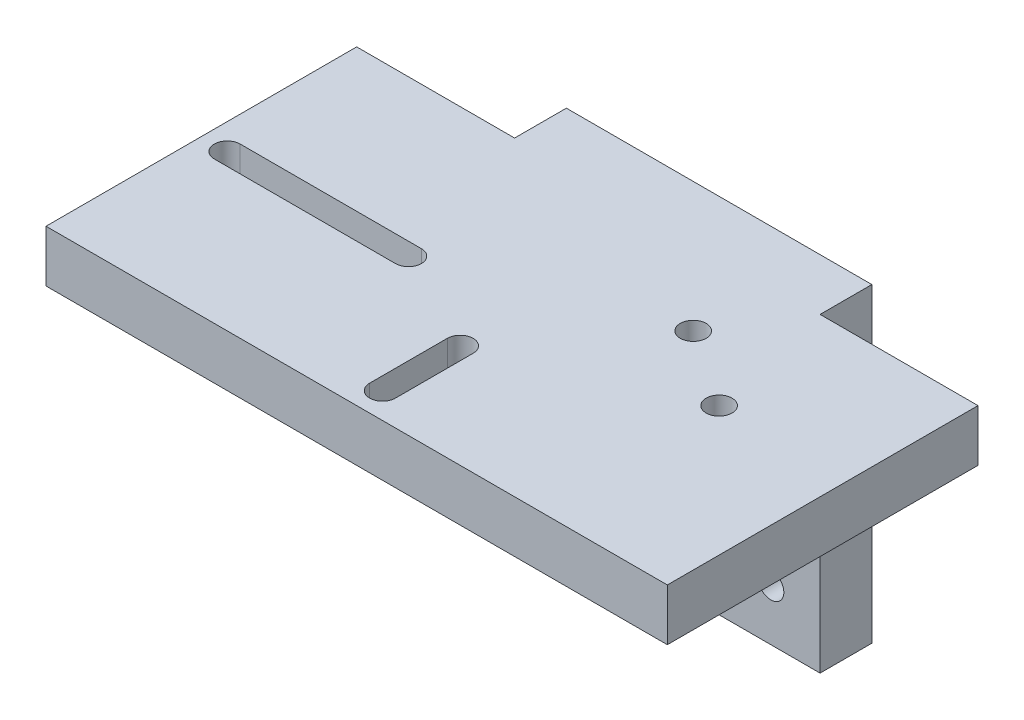
SolidWorks part; units mm, degrees
ref_plane "Front Plane" through (0, 0, 0) normal (0, 0, 1) x (1, 0, 0)
ref_plane "Top Plane" through (0, 0, 0) normal (0, 1, 0) x (1, 0, 0)
ref_plane "Right Plane" through (0, 0, 0) normal (1, 0, 0) x (0, 0, -1)
sketch "Sketch1" plane through (0, 0, 0) normal (0, 0, 1) x (1, 0, 0)
  line L0 (-29.5, 25) -> (-29.5, 35)
  line L1 (-29.5, -25) -> (29.5, -25)
  line L2 (-29.5, -25) -> (-29.5, 25)
  line L3 (-29.5, 25) -> (29.5, 25) construction
  line L4 (29.5, -25) -> (29.5, 25)
  line L5 (-29.5, -25) -> (29.5, 25) construction
  line L6 (-29.5, 25) -> (29.5, -25) construction
  line L7 (20, -15) -> (-20, -15) construction
  line L8 (20, -15) -> (20, 15) construction
  line L9 (20, 15) -> (-20, 15) construction
  line L10 (-20, -15) -> (-20, 15) construction
  line L11 (20, -15) -> (-20, 15) construction
  line L12 (20, 15) -> (-20, -15) construction
  line L13 (-29.5, 35) -> (29.5, 35)
  line L14 (29.5, 35) -> (29.5, 25)
  circle A0 centre (-20, 15) radius 2.5
  circle A1 centre (20, 15) radius 2.5
  circle A2 centre (20, -15) radius 2.5
  circle A3 centre (-20, -15) radius 2.5
  point P0 (0, 0)
  point P6 (0, 0)
  dimension "D5" = 5
  dimension "D6" = 10
  dimension "D1" = 50
  dimension "D2" = 59
  dimension "D3" = 30
  dimension "D4" = 40
extrude "Boss-Extrude1" add sketch "Sketch1" along normal blind 10
sketch "Sketch2" plane through (0, 35, 0) normal (0, 1, 0) x (1, 0, 0)
  line L0 (0, -5.5) -> (0, 5.5) construction
  line L1 (-60, -70) -> (60, -70)
  line L2 (-60, -70) -> (-60, -10)
  line L3 (-60, -10) -> (60, -10)
  line L4 (60, -70) -> (60, -10)
  line L5 (-60, -70) -> (60, -10) construction
  line L6 (-60, -10) -> (60, -70) construction
  line L7 (29.5, -10) -> (-29.5, -10) construction
  line L8 (-55, -37.5) -> (-20, -37.5)
  line L9 (-55, -42.5) -> (-20, -42.5)
  line L10 (-2.5, -65) -> (-2.5, -50)
  line L11 (2.5, -65) -> (2.5, -50)
  circle A0 centre (20, -25) radius 2.5
  circle A1 centre (35, -35) radius 2.5
  arc A2 (2.5, -65) -> (-2.5, -65) centre (0, -65) cw
  arc A3 (-55, -42.5) -> (-55, -37.5) centre (-55, -40) cw
  arc A4 (-20, -37.5) -> (-20, -42.5) centre (-20, -40) cw
  arc A5 (-2.5, -50) -> (2.5, -50) centre (0, -50) cw
  point P0 (0, -40)
  dimension "D3" = 5
  dimension "D8" = 2.5
  dimension "D11" = 2.5
  dimension "D1" = 120
  dimension "D2" = 60
  dimension "D4" = 15
  dimension "D5" = 40
  dimension "D6" = 25
  dimension "D7" = 25
  dimension "D9" = 5
  dimension "D10" = 5
  dimension "D12" = 35
  dimension "D13" = 15
extrude "Boss-Extrude2" add sketch "Sketch2" against normal blind 10
ref_plane "Plane2" through (14.5, 0, 0) normal (1, 0, 0) x (0, 0, -1)
sketch "Sketch4" plane through (14.5, 0, 0) normal (1, 0, 0) x (0, 0, -1)
  line L0 (-10, -5) -> (-10, 35) construction
  line L2 (-70, 25) -> (-10, 25) construction
  line L3 (-40, 25) -> (-10, 25)
  line L4 (-10, -25) -> (-10, 25) construction
  line L5 (-10, -25) -> (0, -25) construction
  line L6 (-10, 25) -> (-10, -5)
  line L7 (-40, 25) -> (-10, -5)
  dimension "D3" = 20
extrude "Boss-Extrude3" add sketch "Sketch4" against normal blind 10
mirror "Mirror1" about plane through (0, 0, 0) normal (1, 0, 0) of "Boss-Extrude3"
